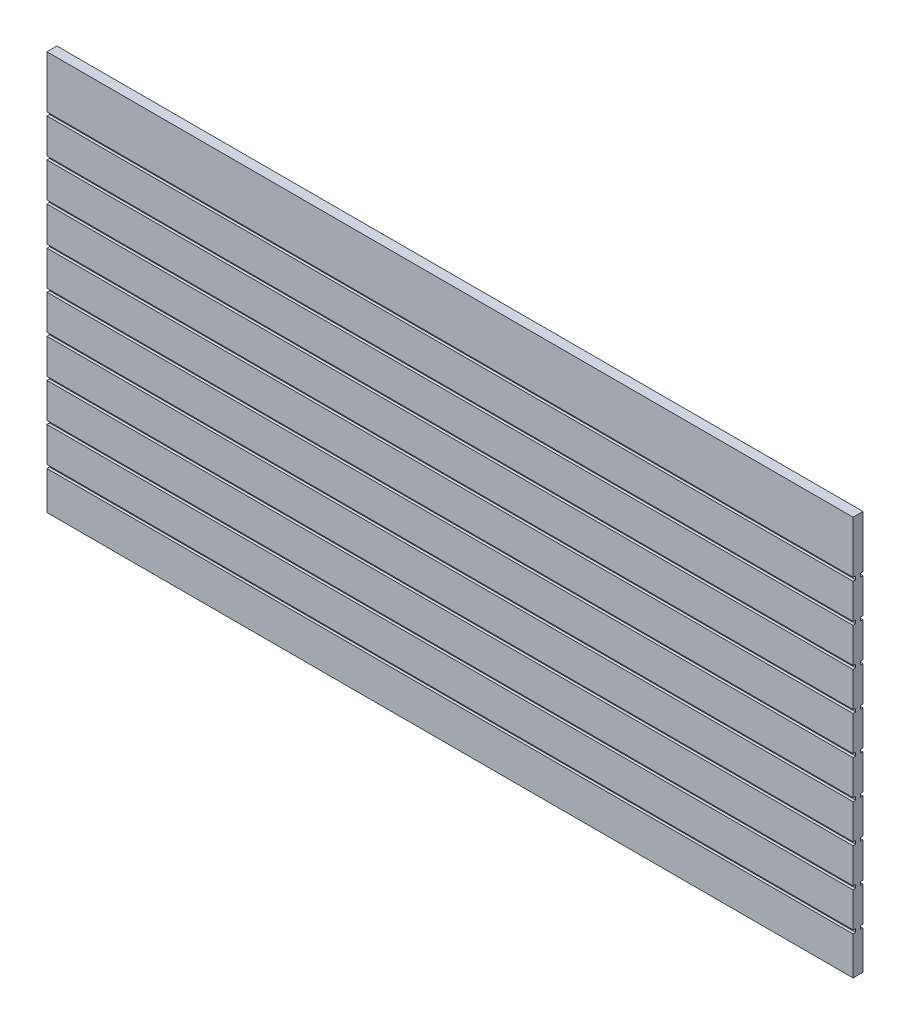
SolidWorks part; units mm, degrees
ref_plane "Front Plane" through (0, 0, 0) normal (0, 0, 1) x (1, 0, 0)
ref_plane "Top Plane" through (0, 0, 0) normal (0, 1, 0) x (1, 0, 0)
ref_plane "Right Plane" through (0, 0, 0) normal (1, 0, 0) x (0, 0, -1)
sketch "Sketch1" plane through (0, 0, 0) normal (0, 0, 1) x (1, 0, 0)
  line L1 (-737.6583, -365.125) -> (737.6583, -365.125)
  line L2 (-737.6583, -365.125) -> (-737.6583, 365.125)
  line L3 (-737.6583, 365.125) -> (737.6583, 365.125)
  line L4 (737.6583, -365.125) -> (737.6583, 365.125)
  line L5 (-737.6583, -365.125) -> (737.6583, 365.125) construction
  line L6 (-737.6583, 365.125) -> (737.6583, -365.125) construction
  point P0 (0, 0)
  dimension "D1" = 730.25
extrude "Boss-Extrude1" add sketch "Sketch1" along normal blind 9.1281 and the other way blind 9.1281
sketch "Sketch2" plane through (0, 0, 9.1281) normal (0, 0, 1) x (1, 0, 0)
  line L0 (-737.6583, 365.125) -> (-737.6583, -365.125) construction
  line L1 (737.6583, -365.125) -> (737.6583, 365.125) construction
  line L2 (-737.6583, -295.275) -> (737.6583, -295.275)
  line L3 (-737.6583, -295.275) -> (-737.6583, -288.925)
  line L4 (-737.6583, -288.925) -> (737.6583, -288.925)
  line L5 (737.6583, -295.275) -> (737.6583, -288.925)
  line L6 (-737.6583, -365.125) -> (737.6583, -365.125) construction
  line L7 (-737.6583, -225.425) -> (737.6583, -225.425)
  line L8 (-737.6583, -225.425) -> (-737.6583, -219.075)
  line L9 (-737.6583, -219.075) -> (737.6583, -219.075)
  line L10 (737.6583, -225.425) -> (737.6583, -219.075)
  line L11 (-737.6583, -155.575) -> (737.6583, -155.575)
  line L12 (-737.6583, -155.575) -> (-737.6583, -149.225)
  line L13 (-737.6583, -149.225) -> (737.6583, -149.225)
  line L14 (737.6583, -155.575) -> (737.6583, -149.225)
  line L15 (-737.6583, -85.725) -> (737.6583, -85.725)
  line L16 (-737.6583, -85.725) -> (-737.6583, -79.375)
  line L17 (-737.6583, -79.375) -> (737.6583, -79.375)
  line L18 (737.6583, -85.725) -> (737.6583, -79.375)
  line L19 (-737.6583, -15.875) -> (737.6583, -15.875)
  line L20 (-737.6583, -15.875) -> (-737.6583, -9.525)
  line L21 (-737.6583, -9.525) -> (737.6583, -9.525)
  line L22 (737.6583, -15.875) -> (737.6583, -9.525)
  line L23 (-737.6583, 53.975) -> (737.6583, 53.975)
  line L24 (-737.6583, 53.975) -> (-737.6583, 60.325)
  line L25 (-737.6583, 60.325) -> (737.6583, 60.325)
  line L26 (737.6583, 53.975) -> (737.6583, 60.325)
  line L27 (-737.6583, 123.825) -> (737.6583, 123.825)
  line L28 (-737.6583, 123.825) -> (-737.6583, 130.175)
  line L29 (-737.6583, 130.175) -> (737.6583, 130.175)
  line L30 (737.6583, 123.825) -> (737.6583, 130.175)
  line L31 (-737.6583, 193.675) -> (737.6583, 193.675)
  line L32 (-737.6583, 193.675) -> (-737.6583, 200.025)
  line L33 (-737.6583, 200.025) -> (737.6583, 200.025)
  line L34 (737.6583, 193.675) -> (737.6583, 200.025)
  line L35 (-737.6583, 263.525) -> (737.6583, 263.525)
  line L36 (-737.6583, 263.525) -> (-737.6583, 269.875)
  line L37 (-737.6583, 269.875) -> (737.6583, 269.875)
  line L38 (737.6583, 263.525) -> (737.6583, 269.875)
  dimension "D1" = 6.35
  dimension "D2" = 69.85
  dimension "D3" = 9
extrude "Cut-Extrude1" cut sketch "Sketch2" against normal blind 4.7625
mirror "Mirror1" about plane through (0, 0, 0) normal (0, 0, 1) of "Cut-Extrude1"
